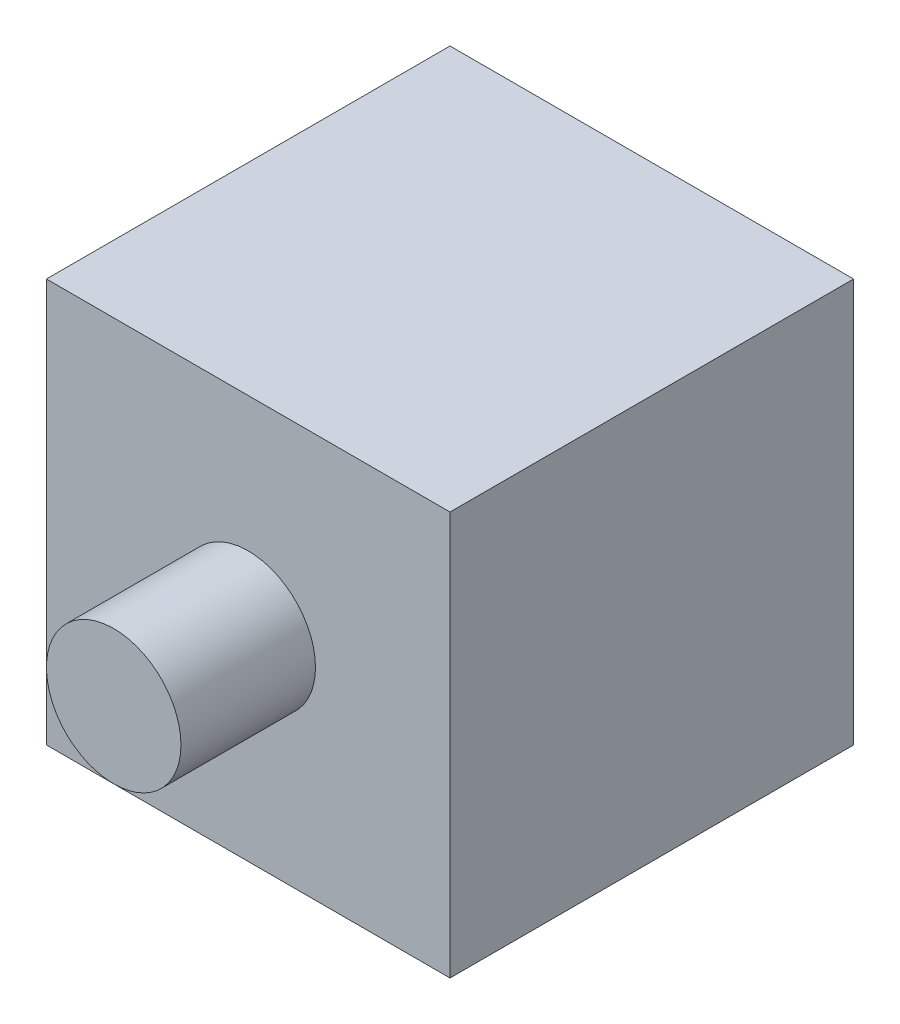
SolidWorks part; units mm, degrees
ref_plane "Front Plane" through (0, 0, 0) normal (0, 0, 1) x (1, 0, 0)
ref_plane "Top Plane" through (0, 0, 0) normal (0, 1, 0) x (1, 0, 0)
ref_plane "Right Plane" through (0, 0, 0) normal (1, 0, 0) x (0, 0, -1)
sketch "Sketch1" plane through (0, 0, 0) normal (0, 1, 0) x (1, 0, 0)
  line L1 (-15, 15) -> (15, 15)
  line L2 (-15, 15) -> (-15, -15)
  line L3 (-15, -15) -> (15, -15)
  line L4 (15, 15) -> (15, -15)
  line L5 (-15, 15) -> (15, -15) construction
  line L6 (-15, -15) -> (15, 15) construction
  point P0 (0, 0)
  dimension "D1" = 30
extrude "Boss-Extrude1" add sketch "Sketch1" along normal blind 30
sketch "Sketch2" plane through (0, 0, 15) normal (0, 0, 1) x (1, 0, 0)
  line L0 (15, 30) -> (-15, 0) construction
  line L1 (-15, 30) -> (15, 0) construction
  circle A0 centre (0, 15) radius 5
  point P11 (0, 15)
  dimension "D1" = 10
extrude "Boss-Extrude2" add sketch "Sketch2" along normal blind 10 contours A0
